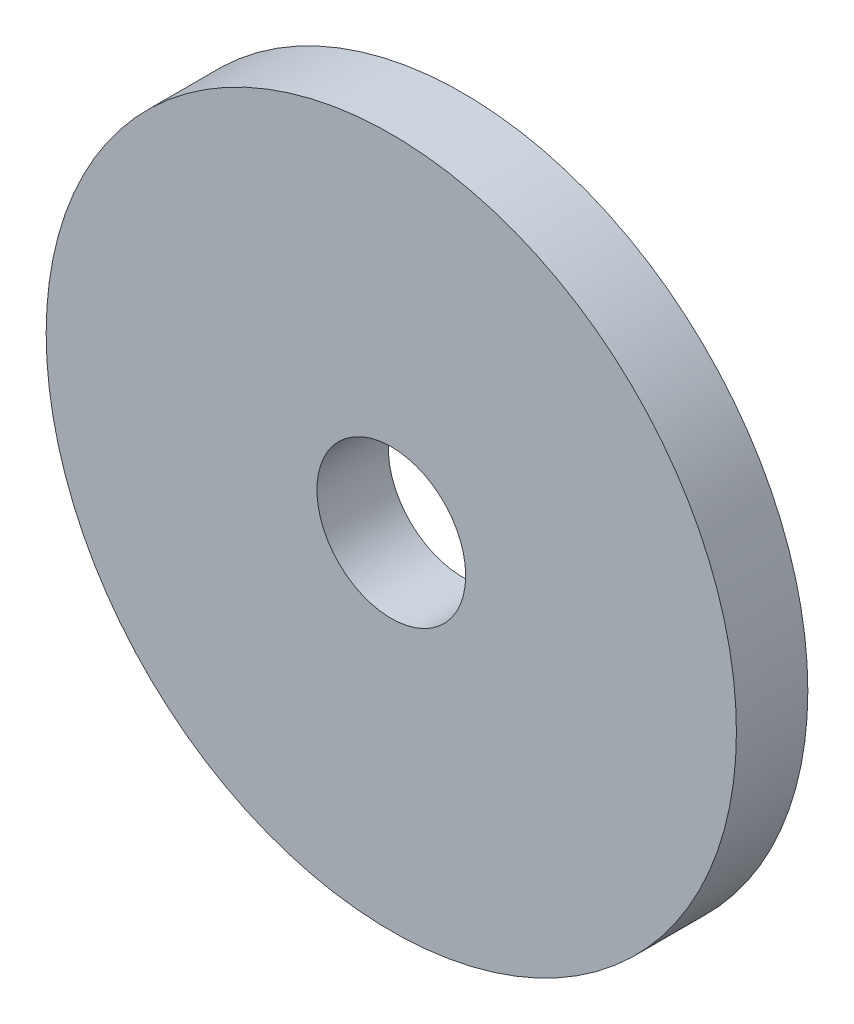
SolidWorks part; units mm, degrees
ref_plane "Front Plane" through (0, 0, 0) normal (0, 0, 1) x (1, 0, 0)
ref_plane "Top Plane" through (0, 0, 0) normal (0, 1, 0) x (1, 0, 0)
ref_plane "Right Plane" through (0, 0, 0) normal (1, 0, 0) x (0, 0, -1)
sketch "Sketch1" plane through (0, 0, 0) normal (0, 0, 1) x (1, 0, 0)
  circle A0 centre (0, 0) radius 14.732
  circle A1 centre (0, 0) radius 6.35
  circle A2 centre (0, 0) radius 9.525 construction
  circle A3 centre (0, 9.525) radius 1.778
  circle A4 centre (6.7352, 6.7352) radius 1.778
  circle A5 centre (9.525, 0) radius 1.778
  circle A6 centre (6.7352, -6.7352) radius 1.778
  circle A7 centre (0, -9.525) radius 1.778
  circle A8 centre (-6.7352, -6.7352) radius 1.778
  circle A9 centre (-9.525, 0) radius 1.778
  circle A10 centre (-6.7352, 6.7352) radius 1.778
  point P23 (0, 0)
  dimension "D1" = 29.464
  dimension "D2" = 12.7
  dimension "D3" = 19.05
  dimension "D4" = 3.556
  dimension "D5" = 8
extrude "Boss-Extrude1" add sketch "Sketch1" along normal blind 3.048 contours A0
sketch "Sketch2" plane through (0, 0, 3.048) normal (0, 0, 1) x (1, 0, 0)
  circle A0 centre (0, 0) radius 3.175
  dimension "D1" = 6.35
extrude "Cut-Extrude1" cut sketch "Sketch2" against normal blind 3.048
sketch "Sketch3" plane through (0, 0, 3.048) normal (0, 0, 1) x (1, 0, 0)
  circle A0 centre (29.464, 0) radius 14.732
  circle A1 centre (29.464, 43.561) radius 28.829
  dimension "D1" = 29.464
  dimension "D3" = 57.658
  dimension "D2" = 29.464
  dimension "D4" = 43.561
  dimension "D5" = 52.5898
